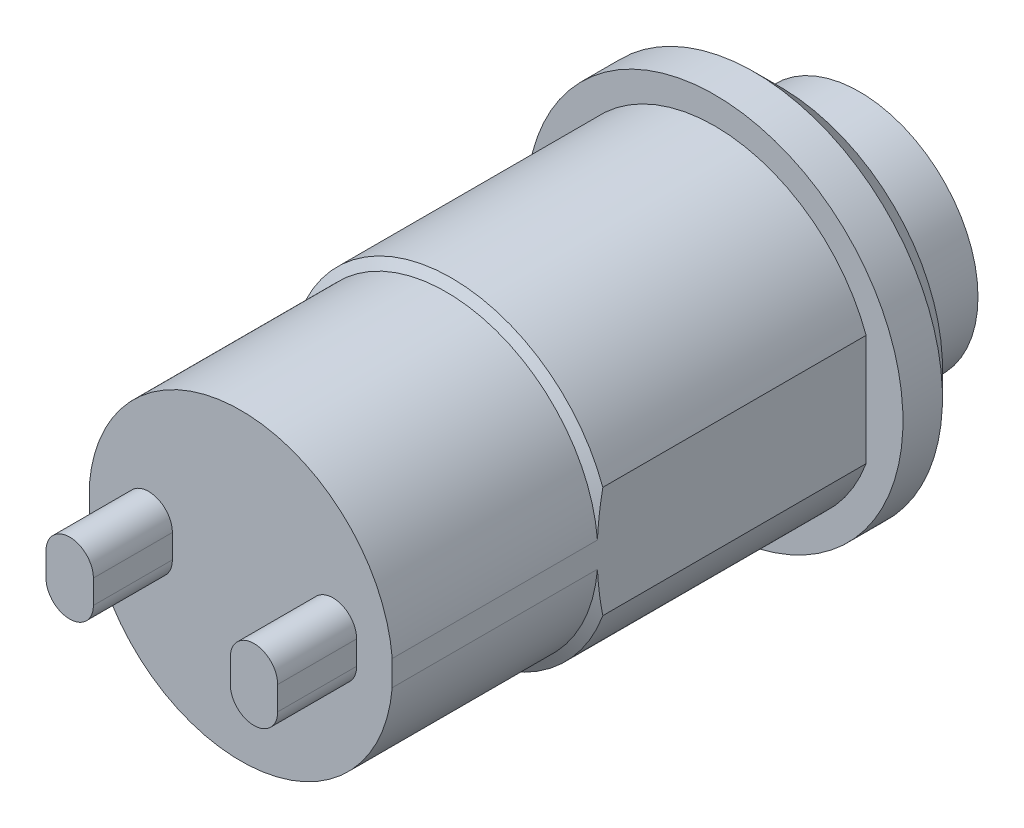
SolidWorks part; units mm, degrees
ref_plane "Front Plane" through (0, 0, 0) normal (0, 0, 1) x (1, 0, 0)
ref_plane "Top Plane" through (0, 0, 0) normal (0, 1, 0) x (1, 0, 0)
ref_plane "Right Plane" through (0, 0, 0) normal (1, 0, 0) x (0, 0, -1)
sketch "Sketch1" plane through (0, 0, 0) normal (0, 1, 0) x (1, 0, 0)
  line L0 (0, 49.6568) -> (0, -58.0069) construction
  line L1 (7.15, 0) -> (6.125, 0)
  line L2 (6.125, 0) -> (6.125, -10)
  line L3 (6.125, -10) -> (5.77, -10.205)
  line L4 (5.77, -10.205) -> (5.77, -18)
  line L5 (5.77, -18) -> (0, -18)
  line L6 (7.15, 0) -> (7.15, 1.5)
  line L7 (7.15, 1.5) -> (6.15, 2.5)
  line L8 (6.15, 2.5) -> (4.5, 2.5)
  line L9 (4.5, 2.5) -> (4.5, 5.5)
  line L10 (4.5, 5.5) -> (0, 5.5) construction
  line L11 (0, -18) -> (0, 6.1)
  arc A0 (0, 6.1) -> (4.5, 5.5) centre (0, -11.075) cw
  dimension "D1" = 11.54
  dimension "D2" = 12.25
  dimension "D3" = 60
  dimension "D4" = 10
  dimension "D6" = 18
  dimension "D7" = 14.3
  dimension "D8" = 2.5
  dimension "D9" = 1.5
  dimension "D10" = 9
  dimension "D11" = 3
  dimension "D12" = 3.6
  dimension "D13" = 45
revolve "Revolve1" add sketch "Sketch1" angle 360 about L0
sketch "Sketch2" plane through (0, 0, 18) normal (0, 0, 1) x (1, 0, 0)
  line L0 (3.5, -0.45) -> (3.5, 0.45) construction
  line L1 (2.6, -0.45) -> (2.6, 0.45)
  line L2 (4.4, -0.45) -> (4.4, 0.45)
  arc A0 (2.6, -0.45) -> (4.4, -0.45) centre (3.5, -0.45) ccw
  arc A1 (4.4, 0.45) -> (2.6, 0.45) centre (3.5, 0.45) ccw
  circle A2 centre (0, 0) radius 5.77 construction
  point P2 (3.5, 0)
  point P7 (3.5, 1.35)
  point P8 (3.5, -1.35)
  dimension "D1" = 2.7
  dimension "D2" = 1.8
  dimension "D3" = 3.5
extrude "Boss-Extrude1" add sketch "Sketch2" along normal blind 3
mirror "Mirror1" about plane through (0, 0, 0) normal (1, 0, 0) of "Boss-Extrude1"
sketch "Sketch3" plane through (0, 0, 18) normal (0, 0, 1) x (1, 0, 0)
  line L0 (5.75, 2.1102) -> (5.75, -2.1102)
  line L1 (-5.75, 0) -> (5.75, 0) construction
  line L2 (-5.75, 2.1102) -> (-5.75, -2.1102)
  arc A0 (5.75, -2.1102) -> (5.75, 2.1102) centre (0, 0) ccw
  circle A1 centre (0, 0) radius 6.125 construction
  arc A5 (-5.75, 2.1102) -> (-5.75, -2.1102) centre (0, 0) ccw
  dimension "D2" = 11.5
extrude "Cut-Extrude1" cut sketch "Sketch3" against normal up to surface (18 mm away) up to face at (-7.15, 0, 0)
